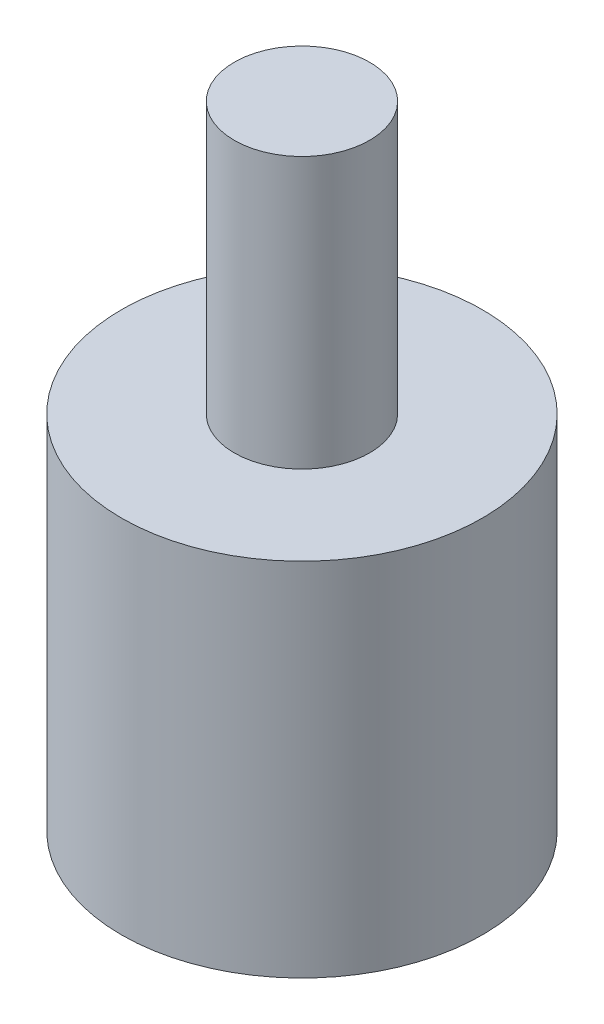
SolidWorks part; units mm, degrees
ref_plane "Front Plane" through (0, 0, 0) normal (0, 0, 1) x (1, 0, 0)
ref_plane "Top Plane" through (0, 0, 0) normal (0, 1, 0) x (1, 0, 0)
ref_plane "Right Plane" through (0, 0, 0) normal (1, 0, 0) x (0, 0, -1)
sketch "Sketch1" plane through (0, 0, 0) normal (0, 1, 0) x (1, 0, 0)
  circle A0 centre (0, 0) radius 1.5
  circle A1 centre (0, 0) radius 4
  dimension "D1" = 3
  dimension "D2" = 8
extrude "Boss-Extrude1" add sketch "Sketch1" along normal blind 8
sketch "Sketch2" plane through (0, 8, 0) normal (0, 1, 0) x (1, 0, 0)
  circle A0 centre (0, 0) radius 1.5
extrude "Boss-Extrude2" add sketch "Sketch2" against normal blind 5
sketch "Sketch3" plane through (0, 8, 0) normal (0, 1, 0) x (1, 0, 0)
  circle A0 centre (0, 0) radius 1.5
  dimension "D1" = 3
extrude "Boss-Extrude3" add sketch "Sketch3" along normal blind 6
